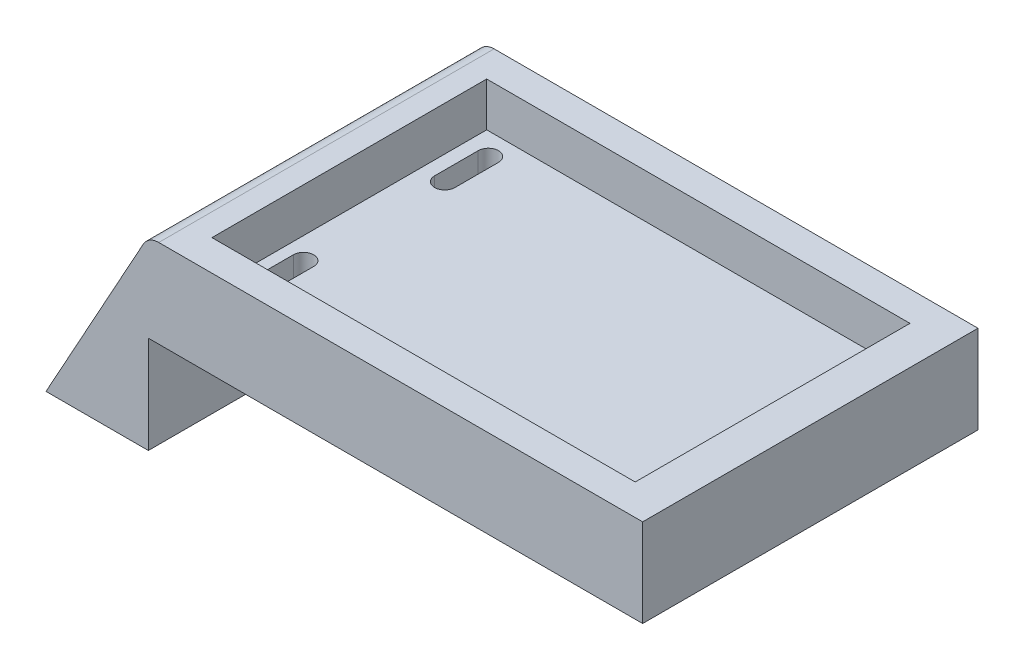
SolidWorks part; units mm, degrees
ref_plane "Front Plane" through (0, 0, 0) normal (0, 0, 1) x (1, 0, 0)
ref_plane "Top Plane" through (0, 0, 0) normal (0, 1, 0) x (1, 0, 0)
ref_plane "Right Plane" through (0, 0, 0) normal (1, 0, 0) x (0, 0, -1)
sketch "Sketch1" plane through (0, 0, 0) normal (0, 1, 0) x (1, 0, 0)
  line L1 (-34.7549, 21.5329) -> (36.5178, 21.5329)
  line L2 (-34.7549, 21.5329) -> (-34.7549, -26.8217)
  line L3 (-34.7549, -26.8217) -> (36.5178, -26.8217)
  line L4 (36.5178, 21.5329) -> (36.5178, -26.8217)
extrude "Boss-Extrude1" add sketch "Sketch1" against normal blind 12.7
sketch "Sketch2" plane through (0, 0, 0) normal (0, 1, 0) x (1, 0, 0)
  line L1 (-30.0271, 17.2356) -> (31.0048, 17.2356)
  line L2 (-30.0271, 17.2356) -> (-30.0271, -22.3816)
  line L3 (-30.0271, -22.3816) -> (31.0048, -22.3816)
  line L4 (31.0048, 17.2356) -> (31.0048, -22.3816)
extrude "Cut-Extrude1" cut sketch "Sketch2" against normal blind 6.35
sketch "Sketch4" plane through (0, 0, 26.8217) normal (0, 0, 1) x (1, 0, 0)
  line L0 (-34.7549, -12.7) -> (-34.7549, -26.7297)
  line L1 (-34.7549, -26.7297) -> (-49.5145, -26.7297)
  line L2 (-49.5145, -26.7297) -> (-34.7549, 0)
  line L3 (-34.7549, 0) -> (-34.7549, -12.7)
extrude "Boss-Extrude2" add sketch "Sketch4" against normal up to surface (48.3546 mm away) up to face at (0.8815, -6.35, -21.5329)
fillet "Fillet1" radius 2.54 1 edges at (-34.7549, 0, 2.6444)
sketch "Sketch5" plane through (0, 0, -21.5329) normal (0, 0, -1) x (-1, 0, 0)
  line L0 (-36.5178, -12.7) -> (34.7549, -12.7) construction
  circle A0 centre (-13.9227, -12.7) radius 7.62
extrude "Cut-Extrude2" cut sketch "Sketch5" against normal blind 2.54
sketch "Sketch7" plane through (0, -6.35, 0) normal (0, 1, 0) x (1, 0, 0)
  line L0 (-26.5747, 14.0285) -> (-26.5747, 7.7385) construction
  line L1 (-25.1099, 14.0285) -> (-25.1099, 7.7385)
  line L2 (-28.0395, 14.0285) -> (-28.0395, 7.7385)
  line L3 (-26.9006, -12.2982) -> (-26.9006, -18.5882) construction
  line L4 (-25.4358, -12.2982) -> (-25.4358, -18.5882)
  line L5 (-28.3654, -12.2982) -> (-28.3654, -18.5882)
  arc A0 (-25.1099, 14.0285) -> (-28.0395, 14.0285) centre (-26.5747, 14.0285) ccw
  arc A1 (-28.0395, 7.7385) -> (-25.1099, 7.7385) centre (-26.5747, 7.7385) ccw
  arc A2 (-25.4358, -12.2982) -> (-28.3654, -12.2982) centre (-26.9006, -12.2982) ccw
  arc A3 (-28.3654, -18.5882) -> (-25.4358, -18.5882) centre (-26.9006, -18.5882) ccw
  point P2 (-26.5747, 10.8835)
  point P7 (0, 0)
  point P10 (-26.9006, -15.4432)
extrude "Cut-Extrude3" cut sketch "Sketch7" against normal up to surface (6.35 mm away) up to face at (6.4496, -12.7, -11.8314)
sketch "Sketch9" plane through (-34.7549, 0, 0) normal (1, 0, 0) x (0, 0, -1)
  line L0 (-2.6444, -26.7297) -> (-2.6444, -13.5483)
  line L1 (21.5329, -26.7297) -> (-26.8217, -26.7297) construction
  line L2 (-2.6444, -13.5483) -> (-0.34, -13.5483)
  line L3 (-0.34, -13.5483) -> (3.5393, -26.7297)
  line L4 (3.5393, -26.7297) -> (-2.6444, -26.7297)
revolve "Cut-Revolve1" cut sketch "Sketch9" angle 180 about L0
